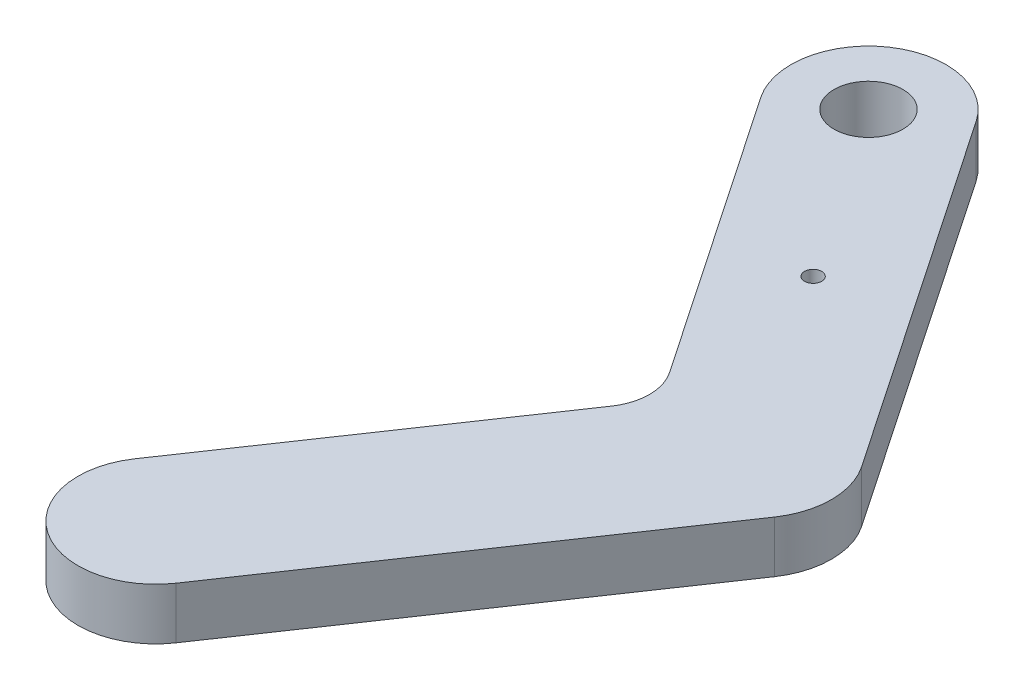
SolidWorks part; units mm, degrees
ref_plane "Front Plane" through (0, 0, 0) normal (0, 0, 1) x (1, 0, 0)
ref_plane "Top Plane" through (0, 0, 0) normal (0, 1, 0) x (1, 0, 0)
ref_plane "Right Plane" through (0, 0, 0) normal (1, 0, 0) x (0, 0, -1)
sketch "Sketch1" plane through (0, 0, 0) normal (0, 1, 0) x (1, 0, 0)
  line L0 (5.0912, -19.4608) -> (5.0912, 21.911) construction
  line L1 (19.1302, 1.2251) -> (5.0912, 21.911) construction
  line L2 (19.1302, 1.2251) -> (5.0912, -19.4608) construction
  line L3 (8.8147, 24.438) -> (22.8537, 3.7521)
  line L4 (1.3678, 19.384) -> (12.5484, 2.9098)
  line L5 (12.5484, -0.4596) -> (1.3678, -16.9338)
  line L6 (8.8147, -21.9878) -> (22.8537, -1.3019)
  line L7 (5.0912, 21.911) -> (19.1302, 1.2251) construction
  line L8 (10.0661, 1.2251) -> (19.1302, 1.2251) construction
  line L9 (5.0912, -19.4608) -> (19.1302, 1.2251) construction
  arc A3 (12.5484, 2.9098) -> (12.5484, -0.4596) centre (10.0661, 1.2251) cw
  arc A4 (1.3678, 19.384) -> (8.8147, 24.438) centre (5.0912, 21.911) cw
  arc A5 (22.8537, 3.7521) -> (22.8537, -1.3019) centre (19.1302, 1.2251) cw
  arc A6 (1.3678, -16.9338) -> (8.8147, -21.9878) centre (5.0912, -19.4608) ccw
  circle A7 centre (5.0912, 21.911) radius 2
  circle A8 centre (11.8777, 11.9114) radius 0.5
  dimension "D4" = 3
  dimension "D5" = 12.085
  dimension "D1" = 9
  dimension "D2" = 9
  dimension "D3" = 25
extrude "Boss-Extrude1" add sketch "Sketch1" along normal blind 3
